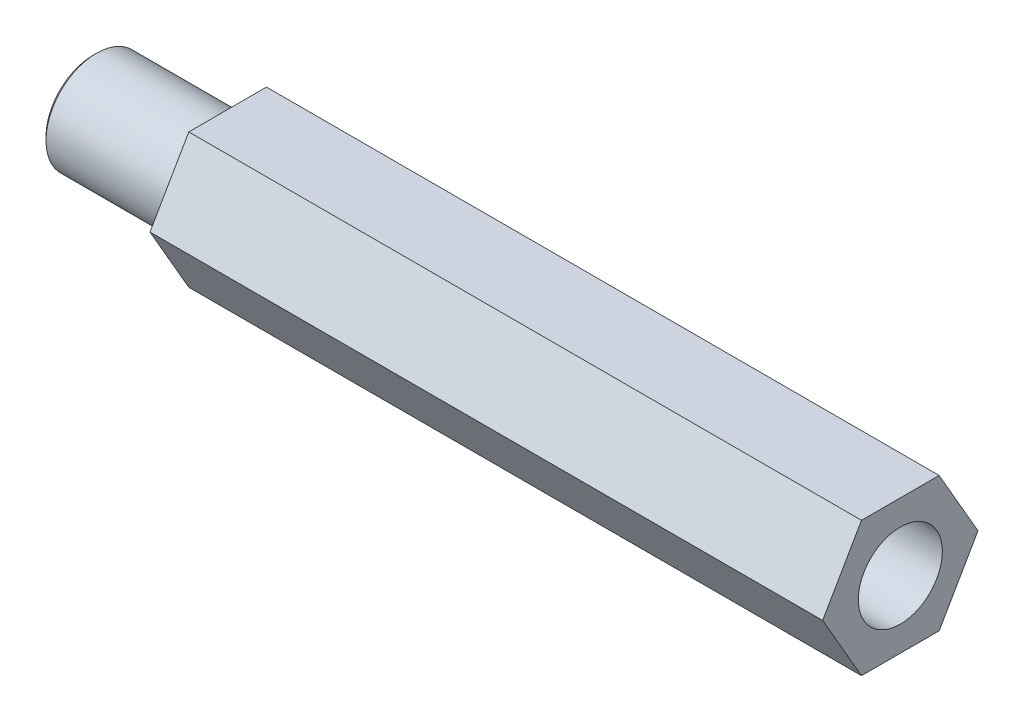
SolidWorks part; units mm, degrees
ref_plane "前视基准面" through (0, 0, 0) normal (0, 0, 1) x (1, 0, 0)
ref_plane "上视基准面" through (0, 0, 0) normal (0, 1, 0) x (1, 0, 0)
ref_plane "右视基准面" through (0, 0, 0) normal (1, 0, 0) x (0, 0, -1)
sketch "草图1" plane through (0, 0, 0) normal (1, 0, 0) x (0, 0, -1)
  line L1 (4.6188, 0) -> (2.3094, 4)
  line L2 (2.3094, 4) -> (-2.3094, 4)
  line L3 (-2.3094, 4) -> (-4.6188, 0)
  line L4 (-4.6188, 0) -> (-2.3094, -4)
  line L5 (-2.3094, -4) -> (2.3094, -4)
  line L6 (2.3094, -4) -> (4.6188, 0)
  circle A0 centre (0, 0) radius 4 construction
  dimension "D1" = 8
extrude "凸台-拉伸1" add sketch "草图1" along normal blind 40
sketch "草图2" plane through (40, 0, 0) normal (1, 0, 0) x (0, 0, -1)
  circle A0 centre (0, 0) radius 2.5
  dimension "D1" = 5
extrude "切除-拉伸1" cut sketch "草图2" against normal blind 12
sketch "草图3" plane through (0, 0, 0) normal (-1, 0, 0) x (0, 0, 1)
  circle A0 centre (0, 0) radius 3
  dimension "D1" = 6
extrude "凸台-拉伸2" add sketch "草图3" along normal blind 8
chamfer "倒角1" distance 0.2 angle 45 1 edges at (-8, 0, 3)
